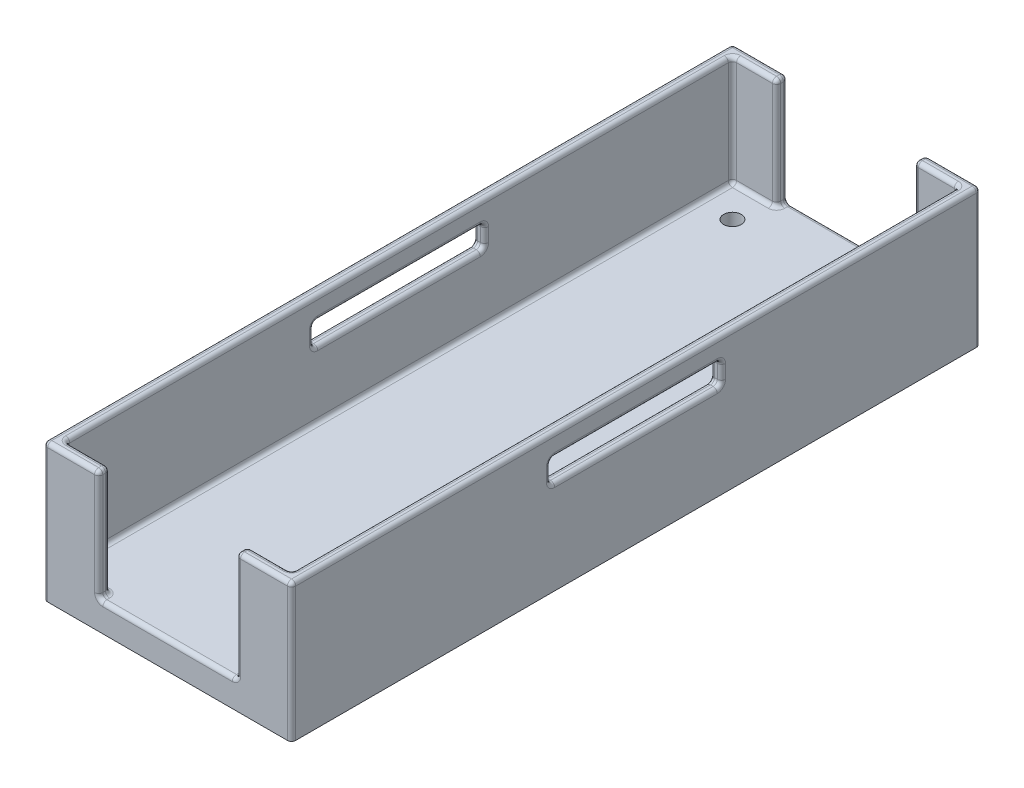
SolidWorks part; units mm, degrees
ref_plane "Front Plane" through (0, 0, 0) normal (0, 0, 1) x (1, 0, 0)
ref_plane "Top Plane" through (0, 0, 0) normal (0, 1, 0) x (1, 0, 0)
ref_plane "Right Plane" through (0, 0, 0) normal (1, 0, 0) x (0, 0, -1)
sketch "Sketch1" plane through (0, 0, 0) normal (0, 1, 0) x (1, 0, 0)
  line L1 (0, 0) -> (45, 0)
  line L2 (0, 0) -> (0, 125)
  line L3 (0, 125) -> (45, 125)
  line L4 (45, 0) -> (45, 125)
  dimension "D1" = 125
  dimension "D2" = 45
extrude "Boss-Extrude1" add sketch "Sketch1" along normal blind 25
sketch "Sketch2" plane through (0, 25, 0) normal (0, 1, 0) x (1, 0, 0)
  line L0 (0, 125) -> (0, 0) construction
  line L1 (2, 123) -> (43, 123)
  line L2 (2, 123) -> (2, 2)
  line L3 (2, 2) -> (43, 2)
  line L4 (43, 123) -> (43, 2)
  line L5 (45, 0) -> (45, 125) construction
  line L6 (45, 125) -> (0, 125) construction
  line L7 (0, 0) -> (45, 0) construction
  dimension "D1" = 2
  dimension "D2" = 2
  dimension "D3" = 2
  dimension "D4" = 2
extrude "Cut-Extrude1" cut sketch "Sketch2" against normal blind 20
sketch "Sketch3" plane through (0, 0, 0) normal (0, 0, 1) x (1, 0, 0)
  line L0 (0, 25) -> (45, 25) construction
  line L1 (10, 25) -> (35, 25)
  line L2 (10, 25) -> (10, 5)
  line L3 (10, 5) -> (35, 5)
  line L4 (35, 25) -> (35, 5)
  line L5 (0, 25) -> (0, 0) construction
  line L6 (45, 25) -> (45, 0) construction
  line L7 (0, 0) -> (45, 0) construction
  dimension "D1" = 10
  dimension "D2" = 10
  dimension "D3" = 5
extrude "Cut-Extrude2" cut sketch "Sketch3" against normal blind 152
sketch "Sketch4" plane through (0, 0, 0) normal (-1, 0, 0) x (0, 0, 1)
  line L0 (-125, 25) -> (0, 25) construction
  line L1 (-78, 21) -> (-47, 21)
  line L2 (-78, 21) -> (-78, 17)
  line L3 (-78, 17) -> (-47, 17)
  line L4 (-47, 21) -> (-47, 17)
  line L5 (0, 25) -> (0, 0) construction
  line L6 (-125, 25) -> (-125, 0) construction
  dimension "D1" = 4
  dimension "D2" = 4
  dimension "D3" = 47
  dimension "D4" = 47
extrude "Cut-Extrude3" cut sketch "Sketch4" against normal blind 126
fillet "Fillet1" radius 0.75 24 edges at (45, 21, -62.5) (43, 21, -62.5) (45, 19, -47) (44, 21, -47) (43, 19, -47) (45, 17, -62.5) (44, 17, -47) (43, 17, -62.5) (45, 19, -78) (44, 17, -78) (43, 19, -78) (44, 21, -78) (2, 19, -78) (0, 19, -78) (2, 19, -47) (0, 19, -47) (2, 21, -62.5) (1, 21, -78) (0, 21, -62.5) (1, 21, -47) (2, 17, -62.5) (1, 17, -47) (0, 17, -62.5) (1, 17, -78)
fillet "Fillet2" radius 0.75 44 edges at (35, 15, 0) (10, 15, 0) (10, 15, -125) (35, 15, -125) (43, 5, -62.5) (39, 5, -2) (35, 5, -1) (22.5, 5, 0) (10, 5, -1) (6, 5, -2) (2, 5, -62.5) (6, 5, -123) (10, 5, -124) (22.5, 5, -125) (35, 5, -124) (39, 5, -123) (45, 25, -62.5) (40, 25, 0) (40, 25, -125) (0, 25, -62.5) (5, 25, -125) (5, 25, 0) (10, 25, -1) (35, 25, -1) (35, 25, -124) (10, 25, -124) (6, 25, -123) (10, 15, -123) (35, 15, -123) (39, 25, -123) (39, 25, -2) (35, 15, -2) (10, 15, -2) (6, 25, -2) (2, 15, -123) (2, 15, -2) (2, 25, -62.5) (43, 15, -2) (43, 15, -123) (43, 25, -62.5) (0, 12.5, -125) (45, 12.5, -125) (45, 12.5, 0) (0, 12.5, 0)
sketch "Sketch5" plane through (0, 5, 0) normal (0, 1, 0) x (1, 0, 0)
  line L0 (2.75, 122.25) -> (2.75, 2.75) construction
  line L1 (9.25, 122.25) -> (2.75, 122.25) construction
  line L2 (42.25, 2.75) -> (42.25, 122.25) construction
  line L3 (35.75, 2.75) -> (42.25, 2.75) construction
  circle A0 centre (7.75, 117.25) radius 1.6
  circle A1 centre (37.25, 7.75) radius 1.6
  dimension "D1" = 3.2
  dimension "D2" = 3.2
  dimension "D3" = 5
  dimension "D4" = 5
  dimension "D5" = 5
  dimension "D6" = 5
extrude "Cut-Extrude4" cut sketch "Sketch5" against normal blind 10
